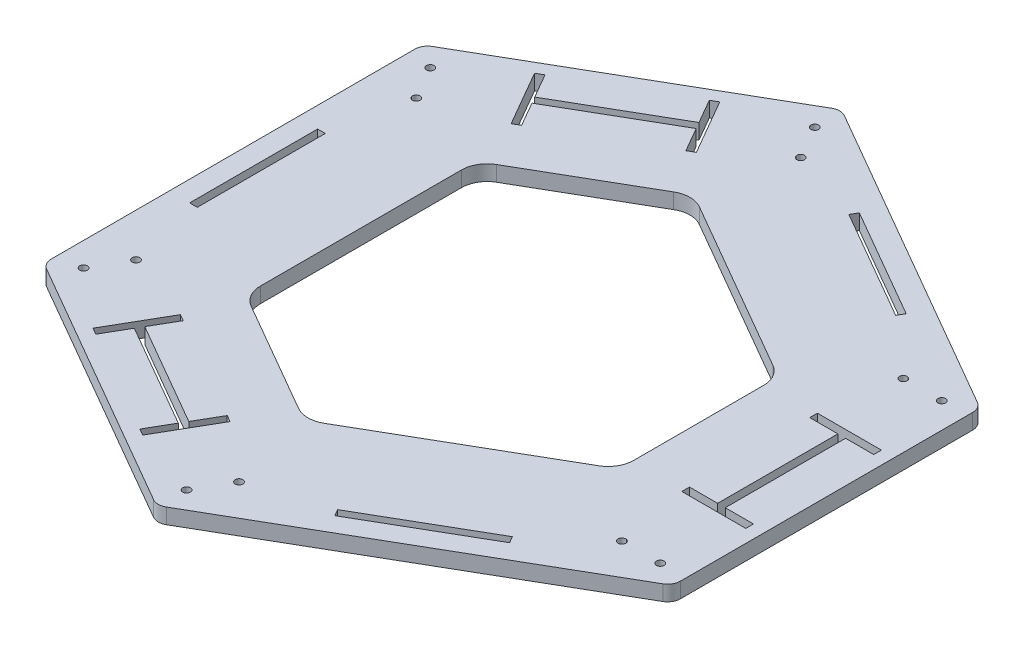
SolidWorks part; units mm, degrees
ref_plane "Front Plane" through (0, 0, 0) normal (0, 0, 1) x (1, 0, 0)
ref_plane "Top Plane" through (0, 0, 0) normal (0, 1, 0) x (1, 0, 0)
ref_plane "Right Plane" through (0, 0, 0) normal (1, 0, 0) x (0, 0, -1)
sketch "Sketch6" plane through (0, 0, 0) normal (0, 1, 0) x (1, 0, 0)
  line L0 (0, 0) -> (154.1474, -77.0737) construction
  line L1 (95, -55) -> (110, -55) construction
  line L2 (95, -55) -> (95, 55) construction
  line L3 (95, 55) -> (110, 55) construction
  line L4 (110, -55) -> (110, 55) construction
  line L5 (95, -55) -> (110, 55) construction
  line L6 (95, 55) -> (110, -55) construction
  line L7 (0, 0) -> (154.1474, 77.0737) construction
  line L8 (0, 0) -> (55.9808, 96.9615)
  line L9 (0, 0) -> (55.9808, -96.9615)
  line L10 (0, 0) -> (180, 0) construction
  line L11 (120, 60) -> (120, -60)
  line L12 (120, 60) -> (55.9808, 96.9615)
  line L13 (120, -60) -> (55.9808, -96.9615)
  circle A0 centre (95, 55) radius 1.5
  circle A1 centre (110, 55) radius 1.5
  circle A2 centre (95, -55) radius 1.5
  circle A3 centre (110, -55) radius 1.5
  point P0 (102.5, 0)
  dimension "D3" = 3
  dimension "D1" = 15
  dimension "D2" = 110
  dimension "D4" = 110
  dimension "D5" = 120
  dimension "D6" = 60
  dimension "D7" = 10
extrude "Boss-Extrude4" add sketch "Sketch6" along normal blind 6
pattern_circular "CirPattern1" count 3 over 360 about axis through (0, 0, 0) along (0, 1, 0) of "Boss-Extrude4"
sketch "Sketch7" plane through (0, 6, 0) normal (0, 1, 0) x (1, 0, 0)
  line L12 (-61.9615, 45.0555) -> (-61.9615, -45.0555)
  line L13 (-61.9615, -45.0555) -> (-8.0385, -76.188)
  line L14 (-8.0385, -76.188) -> (70, -31.1325)
  line L15 (70, -31.1325) -> (70, 31.1325)
  line L16 (70, 31.1325) -> (-8.0385, 76.188)
  line L17 (-8.0385, 76.188) -> (-61.9615, 45.0555)
  line L18 (-61.9615, 45.0555) -> (-61.9615, -45.0555)
  line L19 (-61.9615, -45.0555) -> (-8.0385, -76.188)
  line L20 (-8.0385, -76.188) -> (70, -31.1325)
  line L21 (70, -31.1325) -> (70, 31.1325)
  line L22 (70, 31.1325) -> (-8.0385, 76.188)
  line L23 (-8.0385, 76.188) -> (-61.9615, 45.0555)
  dimension "D1" = 50
sketch "Sketch8" plane through (0, 6, 0) normal (0, 1, 0) x (1, 0, 0)
  line L0 (120, -60) -> (120, 60) construction
  line L1 (103.923, 60) -> (0, 120) construction
  line L2 (0, 120) -> (-103.923, 60) construction
  line L3 (-103.923, 60) -> (-103.923, -60) construction
  line L4 (-103.923, -60) -> (0, -120) construction
  line L5 (0, -120) -> (103.923, -60) construction
  line L6 (103.923, -60) -> (103.923, 60) construction
  line L8 (73.6122, -77.5) -> (30.3109, -102.5)
  line L9 (100.923, 58.2679) -> (0, 116.5359) construction
  line L10 (0, 116.5359) -> (-100.923, 58.2679) construction
  line L11 (-100.923, 58.2679) -> (-100.923, -58.2679) construction
  line L12 (-100.923, -58.2679) -> (0, -116.5359) construction
  line L13 (0, -116.5359) -> (100.923, -58.2679) construction
  line L14 (100.923, -58.2679) -> (100.923, 58.2679) construction
  line L15 (103.923, 25) -> (100.923, 25)
  line L16 (103.923, 25) -> (103.923, -25)
  line L17 (103.923, -25) -> (100.923, -25)
  line L18 (100.923, 25) -> (100.923, -25)
  line L19 (73.6122, -77.5) -> (72.1122, -74.9019)
  line L20 (72.1122, -74.9019) -> (28.8109, -99.9019)
  line L21 (30.3109, -102.5) -> (28.8109, -99.9019)
  line L22 (-30.3109, -102.5) -> (-73.6122, -77.5)
  line L23 (-30.3109, -102.5) -> (-28.8109, -99.9019)
  line L24 (-28.8109, -99.9019) -> (-72.1122, -74.9019)
  line L25 (-73.6122, -77.5) -> (-72.1122, -74.9019)
  line L26 (-103.923, -25) -> (-103.923, 25)
  line L27 (-103.923, -25) -> (-100.923, -25)
  line L28 (-100.923, -25) -> (-100.923, 25)
  line L29 (-103.923, 25) -> (-100.923, 25)
  line L30 (-73.6122, 77.5) -> (-30.3109, 102.5)
  line L31 (-73.6122, 77.5) -> (-72.1122, 74.9019)
  line L32 (-72.1122, 74.9019) -> (-28.8109, 99.9019)
  line L33 (-30.3109, 102.5) -> (-28.8109, 99.9019)
  line L34 (30.3109, 102.5) -> (73.6122, 77.5)
  line L35 (30.3109, 102.5) -> (28.8109, 99.9019)
  line L36 (28.8109, 99.9019) -> (72.1122, 74.9019)
  line L37 (73.6122, 77.5) -> (72.1122, 74.9019)
  circle A0 centre (0, 0) radius 103.923 construction
  circle A1 centre (0, 0) radius 100.923 construction
  point P24 (100.923, 0)
  point P48 (0, 0)
  dimension "D1" = 3
  dimension "D2" = 50
  dimension "D3" = 6
  dimension "D4" = 120
extrude "Cut-Extrude3" cut sketch "Sketch8" against normal through all
extrude "Cut-Extrude4" cut sketch "Sketch7" against normal through all
fillet "Fillet1" radius 10 6 edges at (70, 3, 31.1325) (-8.0385, 3, 76.188) (70, 3, -31.1325) (-8.0385, 3, -76.188) (-61.9615, 3, -45.0555) (-61.9615, 3, 45.0555)
fillet "Fillet2" radius 5 6 edges at (-8.0385, 3, -133.923) (-111.9615, 3, -73.923) (-111.9615, 3, 73.923) (-8.0385, 3, 133.923) (120, 3, -60) (120, 3, 60)
sketch "Sketch9" plane through (0, 6, 0) normal (0, 1, 0) x (1, 0, 0)
  line L0 (120, 0) -> (70, 0) construction
  line L1 (89.923, -26.5) -> (114.923, -26.5)
  line L2 (89.923, -26.5) -> (89.923, -23.5)
  line L3 (89.923, -23.5) -> (114.923, -23.5)
  line L4 (114.923, -26.5) -> (114.923, -23.5)
  line L5 (89.923, 23.5) -> (114.923, 23.5)
  line L6 (89.923, 23.5) -> (89.923, 26.5)
  line L7 (89.923, 26.5) -> (114.923, 26.5)
  line L8 (114.923, 23.5) -> (114.923, 26.5)
  line L9 (120, -57.1132) -> (120, 57.1132) construction
  line L10 (70, -25.359) -> (70, 25.359) construction
  line L11 (100.923, -25) -> (103.923, -25) construction
  line L12 (-67.9112, -64.6256) -> (-65.3131, -66.1256)
  line L13 (-67.9112, -64.6256) -> (-80.4112, -86.2763)
  line L14 (-80.4112, -86.2763) -> (-77.8131, -87.7763)
  line L15 (-65.3131, -66.1256) -> (-77.8131, -87.7763)
  line L16 (-24.6099, -89.6256) -> (-22.0119, -91.1256)
  line L17 (-24.6099, -89.6256) -> (-37.1099, -111.2763)
  line L18 (-37.1099, -111.2763) -> (-34.5119, -112.7763)
  line L19 (-22.0119, -91.1256) -> (-34.5119, -112.7763)
  line L20 (-22.0119, 91.1256) -> (-24.6099, 89.6256)
  line L21 (-22.0119, 91.1256) -> (-34.5119, 112.7763)
  line L22 (-34.5119, 112.7763) -> (-37.1099, 111.2763)
  line L23 (-24.6099, 89.6256) -> (-37.1099, 111.2763)
  line L24 (-65.3131, 66.1256) -> (-67.9112, 64.6256)
  line L25 (-65.3131, 66.1256) -> (-77.8131, 87.7763)
  line L26 (-77.8131, 87.7763) -> (-80.4112, 86.2763)
  line L27 (-67.9112, 64.6256) -> (-80.4112, 86.2763)
  point P8 (114.923, -25)
  point P9 (114.923, 25)
  point P16 (102.423, -26.5)
  point P19 (102.423, -25)
  point P39 (0, 0)
  dimension "D1" = 50
  dimension "D2" = 3
  dimension "D3" = 25
  dimension "D4" = 25
  dimension "D5" = 3
extrude "Cut-Extrude5" cut sketch "Sketch9" against normal through all
